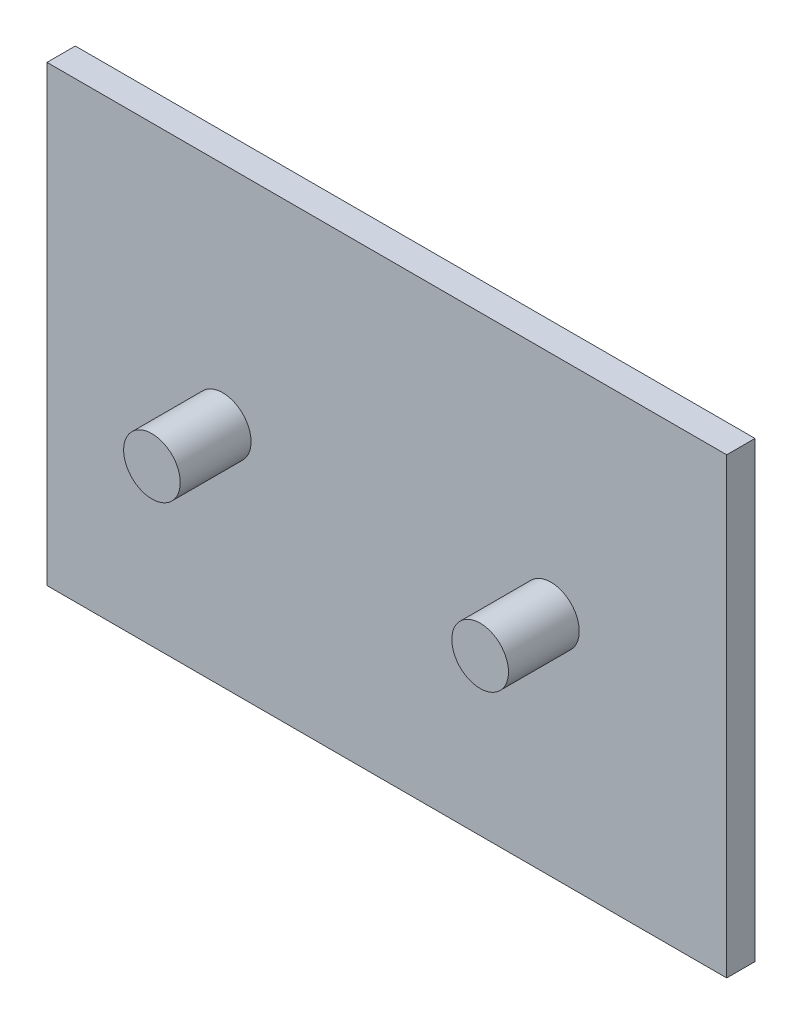
SolidWorks part; units mm, degrees
ref_plane "Front Plane" through (0, 0, 0) normal (0, 0, 1) x (1, 0, 0)
ref_plane "Top Plane" through (0, 0, 0) normal (0, 1, 0) x (1, 0, 0)
ref_plane "Right Plane" through (0, 0, 0) normal (1, 0, 0) x (0, 0, -1)
sketch "Sketch1" plane through (0, 0, 0) normal (0, 0, 1) x (1, 0, 0)
  line L1 (-152.4, -101.6) -> (152.4, -101.6)
  line L2 (-152.4, -101.6) -> (-152.4, 101.6)
  line L3 (-152.4, 101.6) -> (152.4, 101.6)
  line L4 (152.4, -101.6) -> (152.4, 101.6)
  line L5 (-152.4, -101.6) -> (152.4, 101.6) construction
  line L6 (-152.4, 101.6) -> (152.4, -101.6) construction
  point P0 (0, 0)
  dimension "D1" = 304.8
  dimension "D2" = 203.2
extrude "Boss-Extrude1" add sketch "Sketch1" along normal mid plane 12.7
sketch "Sketch2" plane through (0, 0, 6.35) normal (0, 0, 1) x (1, 0, 0)
  line L0 (0, 101.6) -> (0, -101.6) construction
  line L1 (152.4, 101.6) -> (-152.4, 101.6) construction
  line L2 (-152.4, -101.6) -> (152.4, -101.6) construction
  line L3 (-152.4, 0) -> (152.4, 0) construction
  line L4 (-152.4, 101.6) -> (-152.4, -101.6) construction
  line L5 (152.4, -101.6) -> (152.4, 101.6) construction
  circle A0 centre (73.5881, 0) radius 12.7
  circle A1 centre (-73.5881, 0) radius 12.7
  dimension "D1" = 25.4
  dimension "D2" = 73.5881
extrude "Boss-Extrude2" add sketch "Sketch2" along normal blind 31.75
